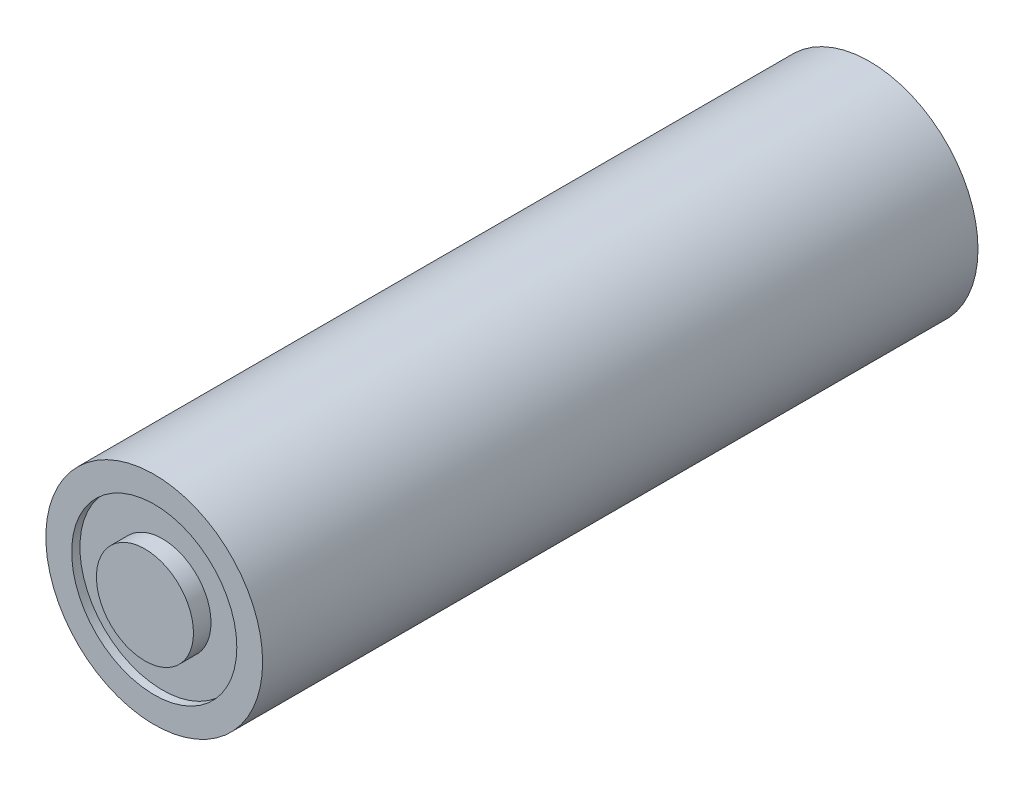
SolidWorks part; units mm, degrees
material "P42A"
ref_plane "X-Y Datum" through (0, 0, 0) normal (0, 0, 1) x (1, 0, 0)
ref_plane "X-Z Datum" through (0, 0, 0) normal (0, 1, 0) x (1, 0, 0)
ref_plane "Y-Z Datum" through (0, 0, 0) normal (1, 0, 0) x (0, 0, -1)
sketch "Sketch1" plane through (0, 0, 0) normal (0, 0, 1) x (1, 0, 0)
  circle A0 centre (0, 0) radius 10.5
extrude "Boss-Extrude1" add sketch "Sketch1" along normal blind 68.5
sketch "Sketch2" plane through (0, 0, 68.5) normal (0, 0, 1) x (1, 0, 0)
  circle A0 centre (0, 0) radius 4.7
extrude "Boss-Extrude2" add sketch "Sketch2" along normal blind 1.7
sketch "Sketch3" plane through (0, 0, 68.5) normal (0, 0, 1) x (1, 0, 0)
  circle A2 centre (0, 0) radius 8
  circle A3 centre (0, 0) radius 8
  circle A4 centre (0, 0) radius 10.5
  dimension "D1" = 2.5
extrude "Boss-Extrude3" add sketch "Sketch3" along normal blind 0.8
